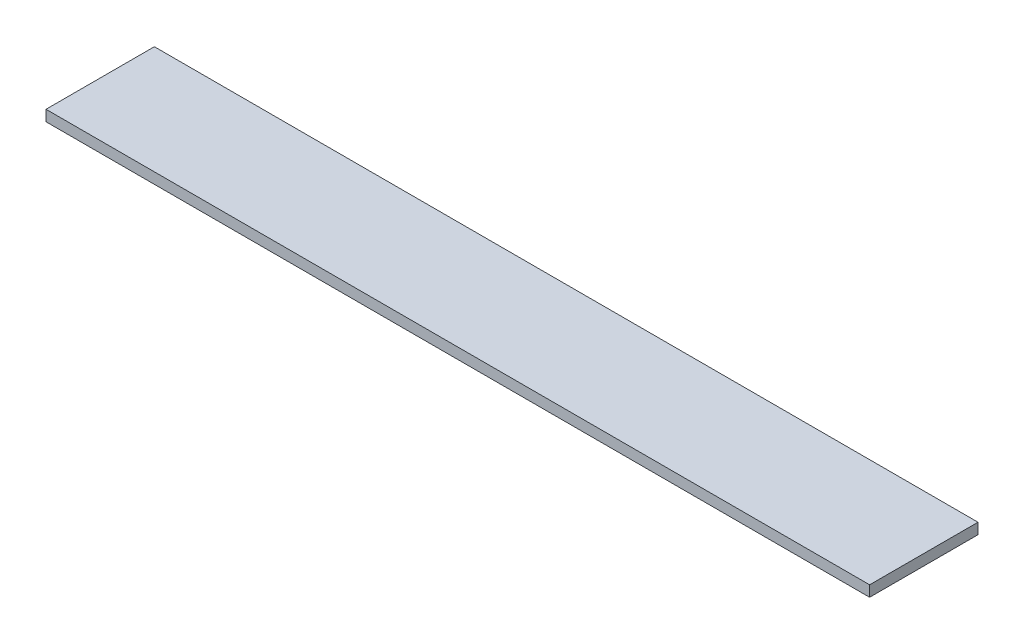
SolidWorks part; units mm, degrees
ref_plane "Front Plane" through (0, 0, 0) normal (0, 0, 1) x (1, 0, 0)
ref_plane "Top Plane" through (0, 0, 0) normal (0, 1, 0) x (1, 0, 0)
ref_plane "Right Plane" through (0, 0, 0) normal (1, 0, 0) x (0, 0, -1)
sketch "Sketch1" plane through (0, 0, 0) normal (0, 1, 0) x (1, 0, 0)
  line L0 (-380, 50) -> (380, -50) construction
  line L1 (-380, 50) -> (380, 50)
  line L2 (-380, 50) -> (-380, -50)
  line L3 (-380, -50) -> (380, -50)
  line L4 (380, 50) -> (380, -50)
  dimension "D1" = 760
  dimension "D2" = 100
extrude "Boss-Extrude1" add sketch "Sketch1" along normal blind 10
